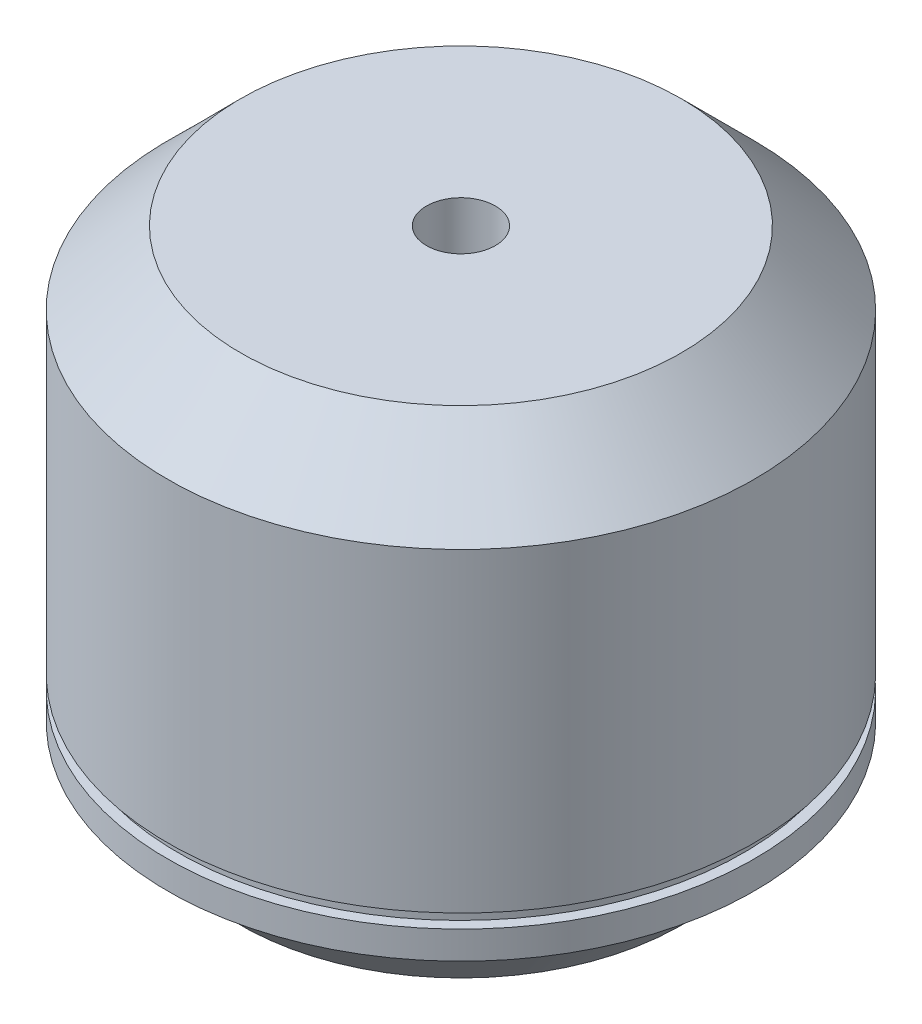
SolidWorks part; units mm, degrees
ref_plane "Plan de face" through (0, 0, 0) normal (0, 0, 1) x (1, 0, 0)
ref_plane "Plan de dessus" through (0, 0, 0) normal (0, 1, 0) x (1, 0, 0)
ref_plane "Plan de droite" through (0, 0, 0) normal (1, 0, 0) x (0, 0, -1)
sketch "Sketch1" plane through (0, 0, 0) normal (0, 0, 1) x (1, 0, 0)
  line L0 (0, 0) -> (0, 36) construction
  line L1 (8, 0) -> (16, 0)
  line L2 (16, 0) -> (20.8, 4.8)
  line L3 (20.8, 4.8) -> (21.3, 4.8)
  line L4 (21.3, 4.8) -> (21.3, 6.822)
  line L5 (21.3, 7.8309) -> (21.3, 30.7)
  line L6 (21.3, 30.7) -> (16, 36)
  line L7 (21.3, 6.822) -> (20.5298, 6.822)
  line L8 (16, 36) -> (2.5, 36)
  line L10 (21.3, 7.8309) -> (20.5298, 7.8309)
  line L11 (20.5298, 6.822) -> (20.5298, 7.8309)
  line L12 (2.5, 36) -> (2.5, 1)
  line L13 (2.5, 1) -> (8, 1)
  line L14 (8, 1) -> (8, 0)
  dimension "D1" = 36
  dimension "D2" = 21.3
  dimension "D3" = 0.5
  dimension "D4" = 45
  dimension "D5" = 16
  dimension "D6" = 16
  dimension "D7" = 5
  dimension "D8" = 8
  dimension "D9" = 1
revolve "Revolve1" add sketch "Sketch1" angle 360 about L0
sketch "Sketch2" plane through (0, 0, 0) normal (0, -1, 0) x (1, 0, 0)
  line L1 (8.8388, -8.8388) -> (-8.8388, -8.8388) construction
  line L2 (8.8388, -8.8388) -> (8.8388, 8.8388) construction
  line L3 (8.8388, 8.8388) -> (-8.8388, 8.8388) construction
  line L4 (-8.8388, -8.8388) -> (-8.8388, 8.8388) construction
  line L5 (8.8388, -8.8388) -> (-8.8388, 8.8388) construction
  line L6 (8.8388, 8.8388) -> (-8.8388, -8.8388) construction
  circle A0 centre (-8.8388, 8.8388) radius 1.5
  circle A1 centre (8.8388, 8.8388) radius 1.5
  circle A2 centre (8.8388, -8.8388) radius 1.5
  circle A3 centre (-8.8388, -8.8388) radius 1.5
  point P0 (0, 0)
  dimension "D2" = 3
  dimension "D1" = 25
extrude "Cut-Extrude1" cut sketch "Sketch2" against normal blind 5
